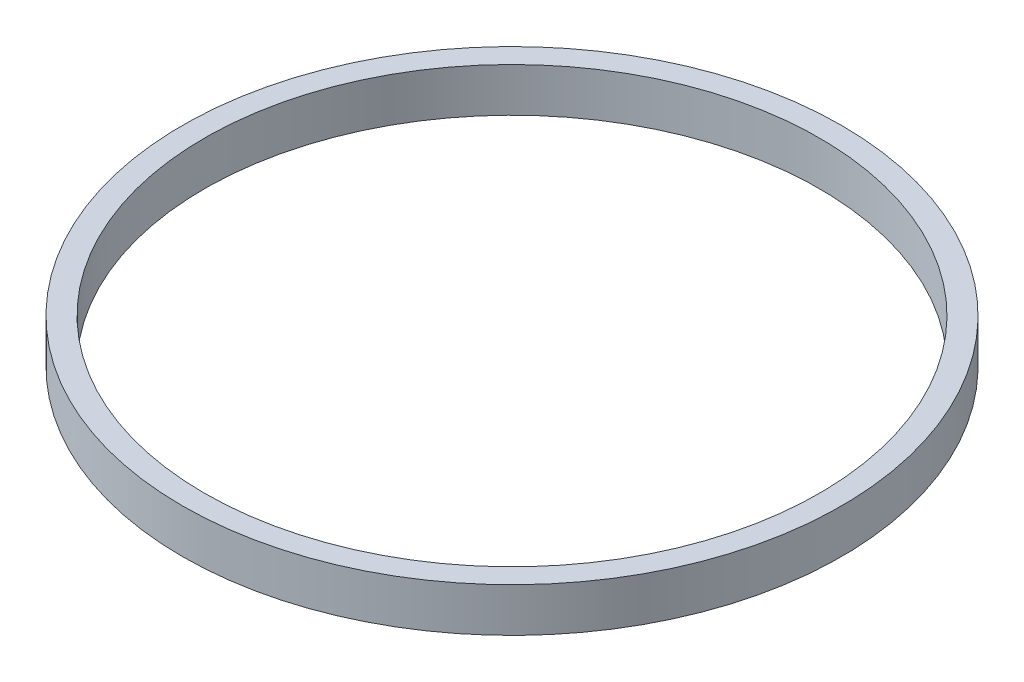
SolidWorks part; units mm, degrees
ref_plane "Front Plane" through (0, 0, 0) normal (0, 0, 1) x (1, 0, 0)
ref_plane "Top Plane" through (0, 0, 0) normal (0, 1, 0) x (1, 0, 0)
ref_plane "Right Plane" through (0, 0, 0) normal (1, 0, 0) x (0, 0, -1)
sketch "Sketch1" plane through (0, 0, 0) normal (0, 1, 0) x (1, 0, 0)
  circle A0 centre (0, 0) radius 225
  dimension "D1" = 450
extrude "Boss-Extrude1" add sketch "Sketch1" along normal blind 30
sketch "Sketch2" plane through (0, 30, 0) normal (0, 1, 0) x (1, 0, 0)
  circle A0 centre (0, 0) radius 210
  dimension "D1" = 420
extrude "Cut-Extrude1" cut sketch "Sketch2" against normal through all both and the other way through all
